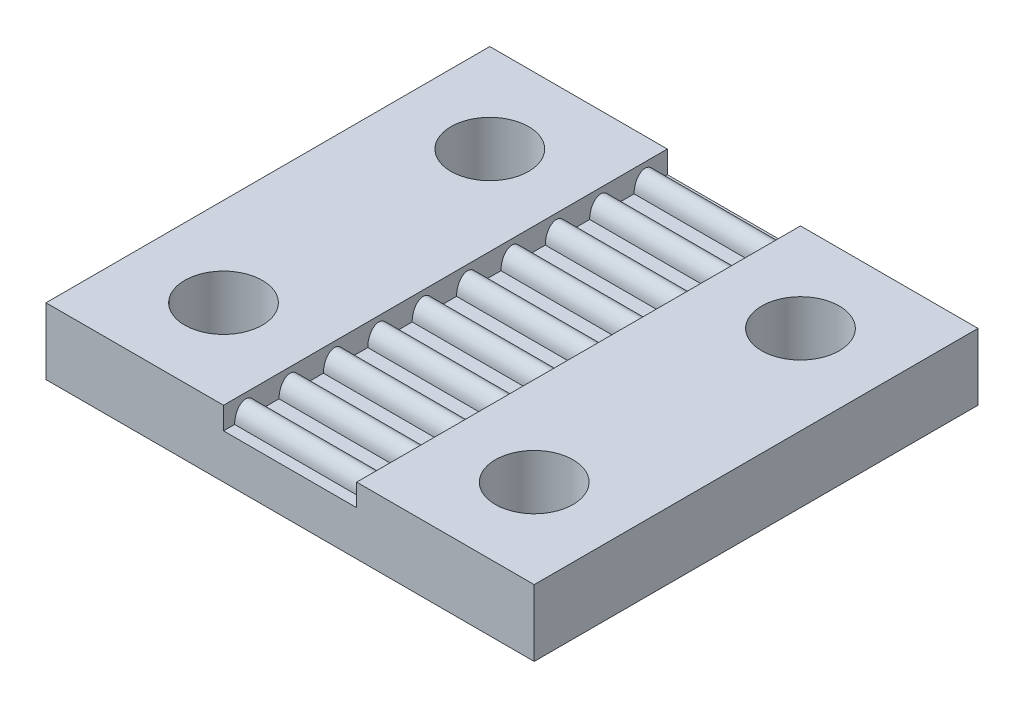
SolidWorks part; units mm, degrees
ref_plane "Front" through (0, 0, 0) normal (0, 0, 1) x (1, 0, 0)
ref_plane "Top" through (0, 0, 0) normal (0, 1, 0) x (1, 0, 0)
ref_plane "Right" through (0, 0, 0) normal (1, 0, 0) x (0, 0, -1)
sketch "Sketch2" plane through (0, 0, 0) normal (0, 0, 1) x (1, 0, 0)
  line L0 (-11, 1) -> (-3, 1)
  line L1 (-11, -2) -> (11, -2)
  line L2 (-11, -2) -> (-11, 1)
  line L4 (11, -2) -> (11, 1)
  line L8 (-3, 1) -> (-3, 0)
  line L9 (-3, 0) -> (3, 0)
  line L10 (3, 1) -> (3, 0)
  line L11 (-3, 1) -> (3, 0) construction
  line L12 (-3, 0) -> (3, 1) construction
  line L13 (3, 1) -> (11, 1)
  point P0 (0, 0)
  point P6 (0, 0.5)
  point P14 (0, -2)
  dimension "D1" = 6
  dimension "D2" = 1
  dimension "D3" = 3
  dimension "D4" = 8
extrude "Boss-Extrude1" add sketch "Sketch2" along normal mid plane 20
sketch "Sketch3" plane through (0, 0, 0) normal (1, 0, 0) x (0, 0, -1)
  ellipse E0 centre (-1, 0) end of major axis (-1, 0.75) minor radius 0.5
  dimension "D1" = 1
  dimension "D3" = 0.5
  dimension "D2" = 1.5
extrude "Boss-Extrude2" add sketch "Sketch3" along normal up to surface (3 mm away) and the other way up to surface (11 mm away) up to face at (3, 0.5, 0)
pattern_linear "LPattern1" count 5 spacing 2 along (0, 0, -1) count 6 spacing 2 along (0, 0, -1) of "Boss-Extrude2"
sketch "Sketch4" plane through (0, 0, 0) normal (0, 1, 0) x (1, 0, 0)
  line L0 (-11, -10) -> (-11, 10) construction
  line L2 (-7, 6) -> (7, 6) construction
  line L3 (-7, 6) -> (-7, -6) construction
  line L4 (-7, -6) -> (7, -6) construction
  line L5 (7, 6) -> (7, -6) construction
  line L6 (-7, 6) -> (7, -6) construction
  line L7 (-7, -6) -> (7, 6) construction
  line L8 (-3, 10) -> (-11, 10) construction
  circle A0 centre (-7, 6) radius 1.75
  circle A1 centre (7, 6) radius 1.75
  circle A2 centre (7, -6) radius 1.75
  circle A3 centre (-7, -6) radius 1.75
  point P4 (0, 0)
  dimension "D4" = 3.5
  dimension "D3" = 4
  dimension "D5" = 4
  dimension "D1" = 2
  dimension "D2" = 2
extrude "Cut-Extrude2" cut sketch "Sketch4" along normal through all both and the other way through all
chamfer "Chamfer1" [suppressed] distance 2.54 angle 45
